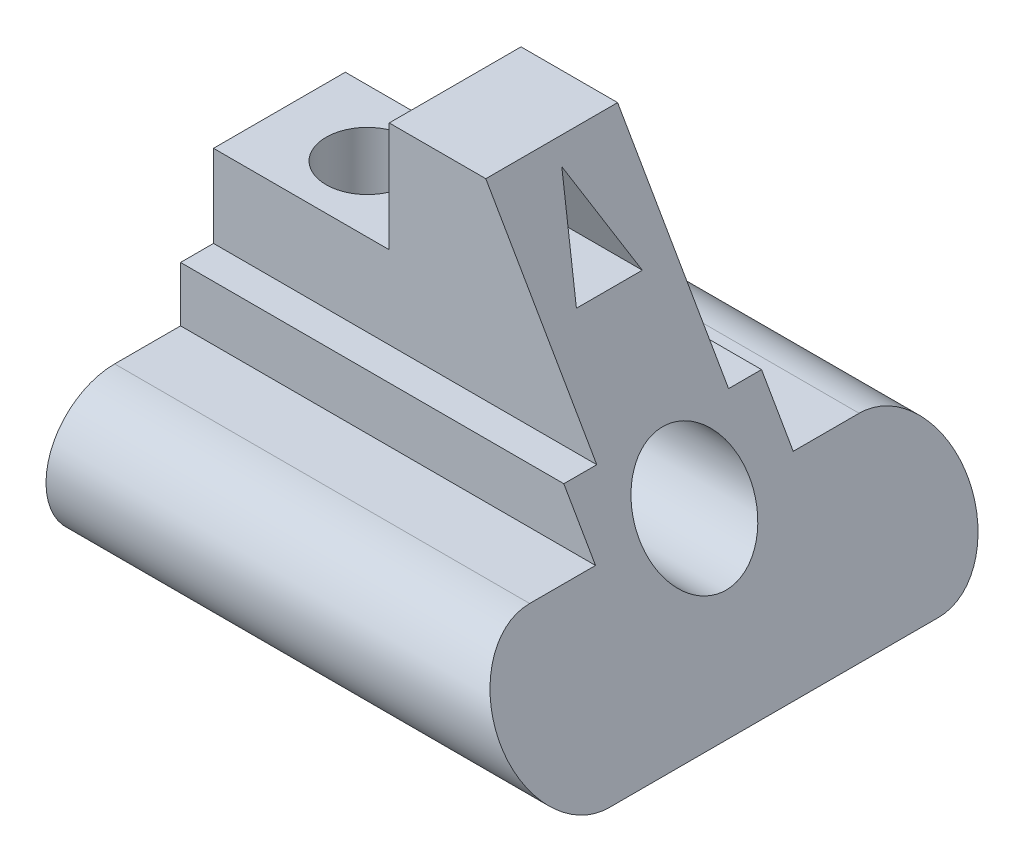
SolidWorks part; units mm, degrees
material "Plain Carbon Steel"
ref_plane "Front Plane" through (0, 0, 0) normal (0, 0, 1) x (1, 0, 0)
ref_plane "Top Plane" through (0, 0, 0) normal (0, 1, 0) x (1, 0, 0)
ref_plane "Right Plane" through (0, 0, 0) normal (1, 0, 0) x (0, 0, -1)
sketch "Sketch3" plane through (0, 0, 0) normal (1, 0, 0) x (0, 0, -1)
  line L0 (-30, 0) -> (30, 0) construction
  line L5 (-30, 12.5) -> (30, 12.5)
  line L6 (-30, -12.5) -> (30, -12.5)
  line L7 (0, 78.6634) -> (0, -41.1587) construction
  line L8 (-18, 12.5) -> (18, 12.5)
  line L9 (-18, 12.5) -> (-18, 22.5)
  line L10 (-18, 22.5) -> (18, 22.5)
  line L11 (18, 12.5) -> (18, 22.5)
  line L12 (-12, 22.5) -> (12, 22.5)
  line L13 (-12, 22.5) -> (-12, 57.5)
  line L14 (-12, 57.5) -> (12, 57.5)
  line L15 (12, 22.5) -> (12, 57.5)
  arc A0 (-30, 12.5) -> (-30, -12.5) centre (-30, 0) ccw
  arc A1 (30, -12.5) -> (30, 12.5) centre (30, 0) ccw
  point P2 (0, 0)
  point P9 (0, 12.5)
  point P13 (0, 22.5)
  dimension "D1" = 12.5
  dimension "D2" = 60
  dimension "D3" = 10
  dimension "D4" = 12
  dimension "D5" = 6
  dimension "D6" = 6
  dimension "D7" = 35
extrude "Boss-Extrude1" add sketch "Sketch3" along normal blind 90 contours L6 A1 L5 A0 | L5 L11 L10 L9 | L10 L15 L14 L13
sketch "Sketch4" plane through (90, 0, 0) normal (1, 0, 0) x (0, 0, -1)
  circle A0 centre (0, 12.5) radius 10
  point P7 (-0.8455, 12.5)
  point P8 (-0.8455, 12.5)
  point P9 (0, 0)
  point P10 (0, 0)
  point P11 (0, 0)
  point P12 (0, 0)
  point P13 (0, 0)
  dimension "D1" = 20
extrude "Cut-Extrude1" cut sketch "Sketch4" against normal through all
sketch "Sketch6" plane through (0, 57.5, 0) normal (0, 1, 0) x (1, 0, 0)
  line L0 (90, -12) -> (0, -12) construction
  line L1 (0, 12) -> (32, 12)
  line L2 (0, 12) -> (0, -12)
  line L3 (0, -12) -> (32, -12)
  line L4 (32, 12) -> (32, -12)
  dimension "D1" = 32
extrude "Cut-Extrude2" cut sketch "Sketch6" against normal blind 20
sketch "Sketch7" plane through (0, 37.5, 0) normal (0, 1, 0) x (1, 0, 0)
  line L1 (16, -8.8402) -> (16, -7.5)
  line L4 (0, 12) -> (0, -12)
  line L5 (0, -12) -> (32, -12)
  line L6 (32, -12) -> (32, 12)
  line L7 (32, 12) -> (0, 12)
  line L8 (0, 12) -> (0, -12)
  line L9 (0, -12) -> (32, -12)
  line L10 (32, -12) -> (32, 12)
  line L11 (32, 12) -> (0, 12)
  circle A0 centre (16, 0) radius 7.5
  dimension "D2" = 15
  dimension "D3" = 16
  dimension "D1" = 0
extrude "Cut-Extrude4" cut sketch "Sketch7" against normal up to next contours A0
sketch "Sketch15" plane through (90, 0, 0) normal (1, 0, 0) x (0, 0, -1)
  line L3 (0, 54.3164) -> (-6, 39.3164)
  line L4 (-6, 39.3164) -> (6, 39.3164)
  line L5 (6, 39.3164) -> (0, 54.3164)
  point P4 (13.8348, 39.3164)
  dimension "D1" = 15
  dimension "D2" = 12
sketch "Sketch9" plane through (0, 0, 12) normal (0, 0, 1) x (1, 0, 0)
  line L20 (90, 22.5) -> (90, 57.5) construction
  line L21 (90, 22.5) -> (90, 57.5)
  line L22 (90, 12.5) -> (90, 22.5) construction
  line L23 (90, 12.5) -> (90, 22.5)
  line L25 (90, -12.5) -> (90, 12.5) construction
  line L26 (90, 57.5) -> (32, 57.5) construction
  line L28 (90, -12.5) -> (90, 12.5)
  line L29 (90, 57.5) -> (49.5855, 57.5)
  line L33 (90, -12.5) -> (49.5855, 57.5)
  dimension "D1" = 30
extrude "Cut-Extrude5" cut sketch "Sketch9" against normal through all both and the other way through all contours L28 L23 L21 L29 L33
sketch "Sketch11" plane through (0, 0, 0) normal (-1, 0, 0) x (0, 0, 1)
extrude "Cut-Extrude6" cut sketch "Sketch15" against normal up to next
